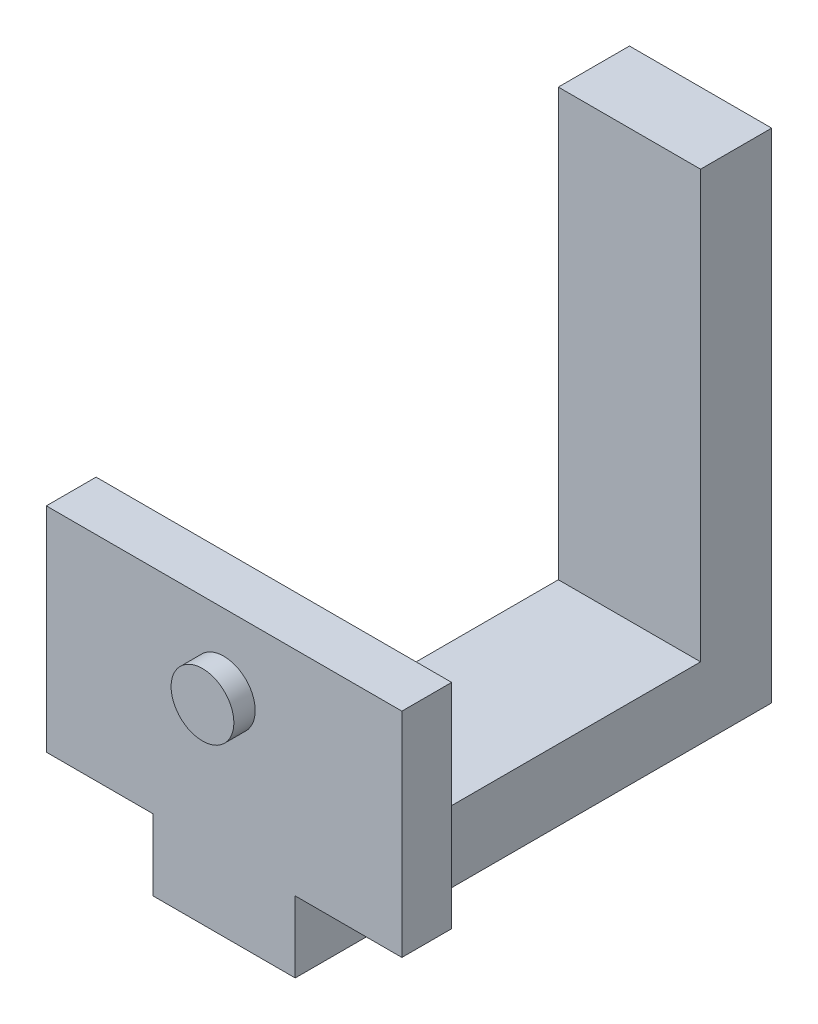
SolidWorks part; units mm, degrees
ref_plane "Front Plane" through (0, 0, 0) normal (0, 0, 1) x (1, 0, 0)
ref_plane "Top Plane" through (0, 0, 0) normal (0, 1, 0) x (1, 0, 0)
ref_plane "Right Plane" through (0, 0, 0) normal (1, 0, 0) x (0, 0, -1)
sketch "Sketch1" plane through (0, 0, 0) normal (0, 0, 1) x (1, 0, 0)
  line L1 (0, 0) -> (20, 0)
  line L2 (0, 0) -> (0, 70)
  line L3 (0, 70) -> (20, 70)
  line L4 (20, 0) -> (20, 70)
  dimension "D1" = 70
  dimension "D2" = 20
extrude "Boss-Extrude1" add sketch "Sketch1" along normal blind 10
sketch "Sketch2" plane through (0, 0, 10) normal (0, 0, 1) x (1, 0, 0)
  line L0 (20, 0) -> (20, 70) construction
  line L1 (0, 0) -> (20, 0)
  line L2 (0, 0) -> (0, 10)
  line L3 (0, 10) -> (20, 10)
  line L4 (20, 0) -> (20, 10)
  dimension "D1" = 10
extrude "Boss-Extrude2" add sketch "Sketch2" along normal blind 50
sketch "Sketch3" plane through (0, 0, 60) normal (0, 0, 1) x (1, 0, 0)
  line L0 (20, 0) -> (20, 10) construction
  line L1 (0, 0) -> (20, 0)
  line L2 (0, 0) -> (0, 10)
  line L3 (0, 10) -> (20, 10)
  line L4 (20, 0) -> (20, 10)
  line L5 (20, 10) -> (0, 10) construction
extrude "Boss-Extrude3" add sketch "Sketch3" along normal blind 7
sketch "Sketch4" plane through (0, 10, 0) normal (0, 1, 0) x (1, 0, 0)
  line L0 (0, -67) -> (0, -10) construction
  line L1 (20, -67) -> (0, -67)
  line L3 (20, -60) -> (0, -60)
  line L5 (20, -60) -> (35, -60)
  line L6 (35, -60) -> (35, -67)
  line L7 (35, -67) -> (20, -67)
  line L8 (0, -67) -> (-15, -67)
  line L9 (-15, -67) -> (-15, -60)
  line L10 (-15, -60) -> (0, -60)
  line L12 (-15, -60) -> (35, -60)
  line L13 (-15, -60) -> (-15, -67)
  line L14 (-15, -67) -> (35, -67)
  line L15 (35, -60) -> (35, -67)
  line M3 (0, -10) -> (0, -67)
  line M4 (0, -67) -> (20, -67)
  line M5 (20, -67) -> (20, -10)
  dimension "D1" = 7
  dimension "D2" = 15
  dimension "D3" = 15
extrude "Boss-Extrude4" add sketch "Sketch4" along normal blind 30 contours L10 L9 L8 M3 | L3 M5 M3 M4 | L7 L6 L5 M5
sketch "Sketch5" plane through (0, 0, 67) normal (0, 0, 1) x (1, 0, 0)
  circle A0 centre (9.9577, 29.7549) radius 4.4145
extrude "Boss-Extrude5" add sketch "Sketch5" along normal blind 3
